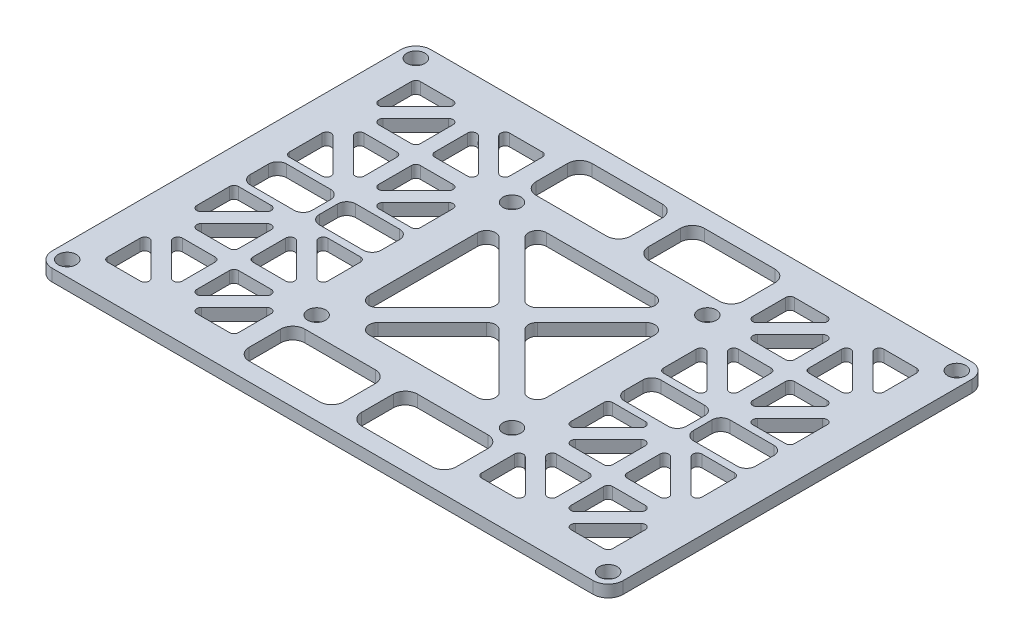
SolidWorks part; units mm, degrees
ref_plane "Front Plane" through (0, 0, 0) normal (0, 0, 1) x (1, 0, 0)
ref_plane "Top Plane" through (0, 0, 0) normal (0, 1, 0) x (1, 0, 0)
ref_plane "Right Plane" through (0, 0, 0) normal (1, 0, 0) x (0, 0, -1)
sketch "Sketch1" plane through (0, 0, 0) normal (0, 1, 0) x (1, 0, 0)
  line L1 (-45, -31.5) -> (45, -31.5)
  line L2 (-47.5, -29) -> (-47.5, 29)
  line L3 (-45, 31.5) -> (45, 31.5)
  line L4 (47.5, -29) -> (47.5, 29)
  line L5 (-47.5, -31.5) -> (47.5, 31.5) construction
  line L6 (-47.5, 31.5) -> (47.5, -31.5) construction
  circle A0 centre (45, 29) radius 1.5
  circle A1 centre (45, -29) radius 1.5
  circle A2 centre (-45, 29) radius 1.5
  circle A3 centre (-45, -29) radius 1.5
  arc A4 (-47.5, 29) -> (-45, 31.5) centre (-45, 29) cw
  arc A5 (-45, -31.5) -> (-47.5, -29) centre (-45, -29) cw
  arc A6 (45, -31.5) -> (47.5, -29) centre (45, -29) ccw
  arc A7 (45, 31.5) -> (47.5, 29) centre (45, 29) cw
  point P0 (0, 0)
  dimension "D3" = 3
  dimension "D5" = 2.5
  dimension "D1" = 95
  dimension "D2" = 63
extrude "Boss-Extrude1" add sketch "Sketch1" along normal blind 2
sketch "Sketch2" plane through (0, 2, 0) normal (0, 1, 0) x (1, 0, 0)
  line L0 (-12.1893, 10.068) -> (-3.182, 1.0607)
  line L1 (-16.25, -16.25) -> (16.25, -16.25) construction
  line L2 (-16.25, -16.25) -> (-16.25, 16.25) construction
  line L3 (-16.25, 16.25) -> (16.25, 16.25) construction
  line L4 (16.25, -16.25) -> (16.25, 16.25) construction
  line L5 (-16.25, -16.25) -> (16.25, 16.25) construction
  line L6 (-16.25, 16.25) -> (16.25, -16.25) construction
  line L7 (-3.182, -1.0607) -> (-12.1893, -10.068)
  line L8 (-14.75, -9.0074) -> (-14.75, 9.0074)
  line L9 (1.0607, 3.182) -> (10.068, 12.1893)
  line L10 (-10.068, 12.1893) -> (-1.0607, 3.182)
  line L11 (9.0074, 14.75) -> (-9.0074, 14.75)
  line L12 (3.182, 1.0607) -> (12.1893, 10.068)
  line L13 (14.75, 9.0074) -> (14.75, -9.0074)
  line L14 (12.1893, -10.068) -> (3.182, -1.0607)
  line L15 (-9.0074, -14.75) -> (9.0074, -14.75)
  line L16 (10.068, -12.1893) -> (1.0607, -3.182)
  line L17 (-1.0607, -3.182) -> (-10.068, -12.1893)
  line L18 (0, -31.5) -> (0, 31.5) construction
  line L19 (45, 31.5) -> (-45, 31.5) construction
  line L20 (35.8327, 26.0221) -> (41.2721, 26.0221)
  line L21 (42.0221, 25.2721) -> (42.0221, 19.8327)
  line L22 (40.7417, 19.3024) -> (35.3024, 24.7417)
  line L23 (33.6053, 23.0447) -> (39.0447, 17.6053)
  line L24 (38.5143, 16.325) -> (33.075, 16.325)
  line L25 (32.325, 17.075) -> (32.325, 22.5143)
  line L26 (31.125, 15.125) -> (14.75, 15.125) construction
  line L27 (40.325, 16.325) -> (42.0221, 18.0221) construction
  line L28 (33.075, 13.925) -> (38.5143, 13.925)
  line L29 (39.0447, 12.6447) -> (33.6053, 7.2053)
  line L30 (32.325, 7.7357) -> (32.325, 13.175)
  line L31 (35.3024, 5.5083) -> (40.7417, 10.9476)
  line L32 (42.0221, 10.4173) -> (42.0221, 4.9779)
  line L33 (41.2721, 4.2279) -> (35.8327, 4.2279)
  line L34 (29.925, 13.175) -> (29.925, 7.7357)
  line L35 (28.6447, 7.2053) -> (23.2053, 12.6447)
  line L36 (23.7357, 13.925) -> (29.175, 13.925)
  line L37 (21.5083, 10.9476) -> (26.9476, 5.5083)
  line L38 (26.4173, 4.2279) -> (20.9779, 4.2279)
  line L39 (20.2279, 4.9779) -> (20.2279, 10.4173)
  line L40 (29.175, 16.325) -> (23.7357, 16.325)
  line L41 (23.2053, 17.6053) -> (28.6447, 23.0447)
  line L42 (29.925, 22.5143) -> (29.925, 17.075)
  line L43 (26.9476, 24.7417) -> (21.5083, 19.3024)
  line L44 (20.2279, 19.8327) -> (20.2279, 25.2721)
  line L45 (20.9779, 26.0221) -> (26.4173, 26.0221)
  line L46 (31.125, 15.125) -> (47.5, 15.125) construction
  line L47 (-45, -31.5) -> (45, -31.5) construction
  line L48 (47.5, -29) -> (47.5, 29) construction
  line L49 (31.125, 15.125) -> (31.125, 31.5) construction
  line L50 (33.075, -16.325) -> (38.5143, -16.325)
  line L51 (39.0447, -17.6053) -> (33.6053, -23.0447)
  line L52 (32.325, -22.5143) -> (32.325, -17.075)
  line L53 (35.3024, -24.7417) -> (40.7417, -19.3024)
  line L54 (42.0221, -19.8327) -> (42.0221, -25.2721)
  line L55 (41.2721, -26.0221) -> (35.8327, -26.0221)
  line L56 (29.925, -17.075) -> (29.925, -22.5143)
  line L57 (28.6447, -23.0447) -> (23.2053, -17.6053)
  line L58 (23.7357, -16.325) -> (29.175, -16.325)
  line L59 (21.5083, -19.3024) -> (26.9476, -24.7417)
  line L60 (26.4173, -26.0221) -> (20.9779, -26.0221)
  line L61 (20.2279, -25.2721) -> (20.2279, -19.8327)
  line L62 (29.175, -13.925) -> (23.7357, -13.925)
  line L63 (23.2053, -12.6447) -> (28.6447, -7.2053)
  line L64 (29.925, -7.7357) -> (29.925, -13.175)
  line L65 (26.9476, -5.5083) -> (21.5083, -10.9476)
  line L66 (20.2279, -10.4173) -> (20.2279, -4.9779)
  line L67 (20.9779, -4.2279) -> (26.4173, -4.2279)
  line L68 (32.325, -13.175) -> (32.325, -7.7357)
  line L69 (33.6053, -7.2053) -> (39.0447, -12.6447)
  line L70 (38.5143, -13.925) -> (33.075, -13.925)
  line L71 (40.7417, -10.9476) -> (35.3024, -5.5083)
  line L72 (35.8327, -4.2279) -> (41.2721, -4.2279)
  line L73 (42.0221, -4.9779) -> (42.0221, -10.4173)
  line L74 (30.525, 0) -> (31.725, 0) construction
  line L81 (21.7279, -3.0279) -> (29.025, -3.0279)
  line L82 (20.2279, -1.5279) -> (20.2279, 1.5279)
  line L83 (21.7279, 3.0279) -> (29.025, 3.0279)
  line L84 (42.0221, -1.5279) -> (42.0221, 1.5279)
  line L85 (20.2279, -3.0279) -> (42.0221, 3.0279) construction
  line L86 (20.2279, 3.0279) -> (42.0221, -3.0279) construction
  line L87 (30.525, -1.5279) -> (30.525, 1.5279)
  line L88 (31.725, -1.5279) -> (31.725, 1.5279)
  line L89 (33.225, 3.0279) -> (40.5221, 3.0279)
  line L90 (33.225, -3.0279) -> (40.5221, -3.0279)
  line L91 (-20.2279, -25.2721) -> (-20.2279, -19.8327)
  line L92 (-26.4173, -26.0221) -> (-20.9779, -26.0221)
  line L93 (-21.5083, -19.3024) -> (-26.9476, -24.7417)
  line L94 (-41.2721, -26.0221) -> (-35.8327, -26.0221)
  line L95 (-42.0221, -19.8327) -> (-42.0221, -25.2721)
  line L96 (-35.3024, -24.7417) -> (-40.7417, -19.3024)
  line L97 (-32.325, -22.5143) -> (-32.325, -17.075)
  line L98 (-39.0447, -17.6053) -> (-33.6053, -23.0447)
  line L99 (-33.075, -16.325) -> (-38.5143, -16.325)
  line L100 (-23.7357, -16.325) -> (-29.175, -16.325)
  line L101 (-28.6447, -23.0447) -> (-23.2053, -17.6053)
  line L102 (-29.925, -17.075) -> (-29.925, -22.5143)
  line L103 (-20.9779, -4.2279) -> (-26.4173, -4.2279)
  line L104 (-20.2279, -10.4173) -> (-20.2279, -4.9779)
  line L105 (-26.9476, -5.5083) -> (-21.5083, -10.9476)
  line L106 (-29.925, -7.7357) -> (-29.925, -13.175)
  line L107 (-23.2053, -12.6447) -> (-28.6447, -7.2053)
  line L108 (-29.175, -13.925) -> (-23.7357, -13.925)
  line L109 (-38.5143, -13.925) -> (-33.075, -13.925)
  line L110 (-33.6053, -7.2053) -> (-39.0447, -12.6447)
  line L111 (-32.325, -13.175) -> (-32.325, -7.7357)
  line L112 (-42.0221, -4.9779) -> (-42.0221, -10.4173)
  line L113 (-35.8327, -4.2279) -> (-41.2721, -4.2279)
  line L114 (-40.7417, -10.9476) -> (-35.3024, -5.5083)
  line L115 (-33.225, -3.0279) -> (-40.5221, -3.0279)
  line L116 (-31.725, -1.5279) -> (-31.725, 1.5279)
  line L117 (-33.225, 3.0279) -> (-40.5221, 3.0279)
  line L118 (-42.0221, -1.5279) -> (-42.0221, 1.5279)
  line L119 (-20.2279, -1.5279) -> (-20.2279, 1.5279)
  line L120 (-21.7279, 3.0279) -> (-29.025, 3.0279)
  line L121 (-30.525, -1.5279) -> (-30.525, 1.5279)
  line L122 (-21.7279, -3.0279) -> (-29.025, -3.0279)
  line L123 (-20.2279, 4.9779) -> (-20.2279, 10.4173)
  line L124 (-26.4173, 4.2279) -> (-20.9779, 4.2279)
  line L125 (-21.5083, 10.9476) -> (-26.9476, 5.5083)
  line L126 (-41.2721, 4.2279) -> (-35.8327, 4.2279)
  line L127 (-42.0221, 10.4173) -> (-42.0221, 4.9779)
  line L128 (-35.3024, 5.5083) -> (-40.7417, 10.9476)
  line L129 (-23.7357, 13.925) -> (-29.175, 13.925)
  line L130 (-28.6447, 7.2053) -> (-23.2053, 12.6447)
  line L131 (-29.925, 13.175) -> (-29.925, 7.7357)
  line L132 (-32.325, 7.7357) -> (-32.325, 13.175)
  line L133 (-39.0447, 12.6447) -> (-33.6053, 7.2053)
  line L134 (-33.075, 13.925) -> (-38.5143, 13.925)
  line L135 (-42.0221, 25.2721) -> (-42.0221, 19.8327)
  line L136 (-35.8327, 26.0221) -> (-41.2721, 26.0221)
  line L137 (-40.7417, 19.3024) -> (-35.3024, 24.7417)
  line L138 (-38.5143, 16.325) -> (-33.075, 16.325)
  line L139 (-33.6053, 23.0447) -> (-39.0447, 17.6053)
  line L140 (-32.325, 17.075) -> (-32.325, 22.5143)
  line L141 (-29.925, 22.5143) -> (-29.925, 17.075)
  line L142 (-23.2053, 17.6053) -> (-28.6447, 23.0447)
  line L143 (-29.175, 16.325) -> (-23.7357, 16.325)
  line L144 (-20.9779, 26.0221) -> (-26.4173, 26.0221)
  line L145 (-20.2279, 19.8327) -> (-20.2279, 25.2721)
  line L146 (-26.9476, 24.7417) -> (-21.5083, 19.3024)
  line L147 (-17.2279, -19.25) -> (-17.2279, -16.25) construction
  line L148 (-15.2279, -28.5) -> (-3.5, -28.5)
  line L149 (-17.2279, -26.5) -> (-17.2279, -21.25)
  line L150 (-15.2279, -19.25) -> (-3.5, -19.25)
  line L151 (17.2279, -26.5) -> (17.2279, -21.25)
  line L152 (-17.2279, -28.5) -> (17.2279, -19.25) construction
  line L153 (-17.2279, -19.25) -> (17.2279, -28.5) construction
  line L154 (-17.2279, -28.5) -> (-17.2279, -31.5) construction
  line L155 (-1.5, -23.875) -> (1.5, -23.875) construction
  line L156 (-1.5, -26.5) -> (-1.5, -21.25)
  line L157 (1.5, -26.5) -> (1.5, -21.25)
  line L158 (3.5, -19.25) -> (15.2279, -19.25)
  line L159 (3.5, -28.5) -> (15.2279, -28.5)
  line L160 (3.5, 28.5) -> (15.2279, 28.5)
  line L161 (1.5, 26.5) -> (1.5, 21.25)
  line L162 (3.5, 19.25) -> (15.2279, 19.25)
  line L163 (17.2279, 26.5) -> (17.2279, 21.25)
  line L164 (-17.2279, 26.5) -> (-17.2279, 21.25)
  line L165 (-15.2279, 19.25) -> (-3.5, 19.25)
  line L166 (-1.5, 26.5) -> (-1.5, 21.25)
  line L167 (-15.2279, 28.5) -> (-3.5, 28.5)
  circle A0 centre (-16.25, 16.25) radius 1.5
  circle A1 centre (-16.25, -16.25) radius 1.5
  circle A2 centre (16.25, 16.25) radius 1.5
  circle A3 centre (16.25, -16.25) radius 1.5
  arc A4 (-14.75, -9.0074) -> (-12.1893, -10.068) centre (-13.25, -9.0074) ccw
  arc A5 (-3.182, -1.0607) -> (-3.182, 1.0607) centre (-4.2426, 0) ccw
  arc A6 (-12.1893, 10.068) -> (-14.75, 9.0074) centre (-13.25, 9.0074) ccw
  arc A7 (1.0607, 3.182) -> (-1.0607, 3.182) centre (0, 4.2426) cw
  arc A8 (9.0074, 14.75) -> (10.068, 12.1893) centre (9.0074, 13.25) cw
  arc A9 (-10.068, 12.1893) -> (-9.0074, 14.75) centre (-9.0074, 13.25) cw
  arc A10 (14.75, 9.0074) -> (12.1893, 10.068) centre (13.25, 9.0074) ccw
  arc A11 (12.1893, -10.068) -> (14.75, -9.0074) centre (13.25, -9.0074) ccw
  arc A12 (3.182, 1.0607) -> (3.182, -1.0607) centre (4.2426, 0) ccw
  arc A13 (10.068, -12.1893) -> (9.0074, -14.75) centre (9.0074, -13.25) cw
  arc A14 (-1.0607, -3.182) -> (1.0607, -3.182) centre (0, -4.2426) cw
  arc A15 (-9.0074, -14.75) -> (-10.068, -12.1893) centre (-9.0074, -13.25) cw
  arc A16 (33.075, 13.925) -> (32.325, 13.175) centre (33.075, 13.175) ccw
  circle A17 centre (45, 29) radius 1.5 construction
  circle A18 centre (45, 29) radius 1.5 construction
  arc A19 (40.7417, 19.3024) -> (42.0221, 19.8327) centre (41.2721, 19.8327) ccw
  arc A20 (42.0221, 25.2721) -> (41.2721, 26.0221) centre (41.2721, 25.2721) ccw
  arc A21 (35.8327, 26.0221) -> (35.3024, 24.7417) centre (35.8327, 25.2721) ccw
  arc A22 (32.325, 17.075) -> (33.075, 16.325) centre (33.075, 17.075) ccw
  arc A23 (38.5143, 16.325) -> (39.0447, 17.6053) centre (38.5143, 17.075) ccw
  arc A24 (33.6053, 23.0447) -> (32.325, 22.5143) centre (33.075, 22.5143) ccw
  arc A25 (20.9779, 26.0221) -> (20.2279, 25.2721) centre (20.9779, 25.2721) ccw
  arc A26 (20.2279, 19.8327) -> (21.5083, 19.3024) centre (20.9779, 19.8327) ccw
  arc A27 (26.9476, 24.7417) -> (26.4173, 26.0221) centre (26.4173, 25.2721) ccw
  arc A28 (28.6447, 23.0447) -> (29.925, 22.5143) centre (29.175, 22.5143) cw
  arc A29 (29.925, 17.075) -> (29.175, 16.325) centre (29.175, 17.075) cw
  arc A30 (23.7357, 16.325) -> (23.2053, 17.6053) centre (23.7357, 17.075) cw
  arc A31 (20.2279, 4.9779) -> (20.9779, 4.2279) centre (20.9779, 4.9779) ccw
  arc A32 (26.4173, 4.2279) -> (26.9476, 5.5083) centre (26.4173, 4.9779) ccw
  arc A33 (21.5083, 10.9476) -> (20.2279, 10.4173) centre (20.9779, 10.4173) ccw
  arc A34 (23.7357, 13.925) -> (23.2053, 12.6447) centre (23.7357, 13.175) ccw
  arc A35 (28.6447, 7.2053) -> (29.925, 7.7357) centre (29.175, 7.7357) ccw
  arc A36 (29.925, 13.175) -> (29.175, 13.925) centre (29.175, 13.175) ccw
  arc A37 (40.7417, 10.9476) -> (42.0221, 10.4173) centre (41.2721, 10.4173) cw
  arc A38 (42.0221, 4.9779) -> (41.2721, 4.2279) centre (41.2721, 4.9779) cw
  arc A39 (35.8327, 4.2279) -> (35.3024, 5.5083) centre (35.8327, 4.9779) cw
  arc A40 (32.325, 7.7357) -> (33.6053, 7.2053) centre (33.075, 7.7357) ccw
  arc A41 (39.0447, 12.6447) -> (38.5143, 13.925) centre (38.5143, 13.175) ccw
  arc A42 (39.0447, -17.6053) -> (38.5143, -16.325) centre (38.5143, -17.075) ccw
  arc A43 (33.075, -16.325) -> (32.325, -17.075) centre (33.075, -17.075) ccw
  arc A44 (32.325, -22.5143) -> (33.6053, -23.0447) centre (33.075, -22.5143) ccw
  arc A45 (35.8327, -26.0221) -> (35.3024, -24.7417) centre (35.8327, -25.2721) cw
  arc A46 (40.7417, -19.3024) -> (42.0221, -19.8327) centre (41.2721, -19.8327) cw
  arc A47 (42.0221, -25.2721) -> (41.2721, -26.0221) centre (41.2721, -25.2721) cw
  arc A48 (29.925, -17.075) -> (29.175, -16.325) centre (29.175, -17.075) ccw
  arc A49 (28.6447, -23.0447) -> (29.925, -22.5143) centre (29.175, -22.5143) ccw
  arc A50 (23.7357, -16.325) -> (23.2053, -17.6053) centre (23.7357, -17.075) ccw
  arc A51 (21.5083, -19.3024) -> (20.2279, -19.8327) centre (20.9779, -19.8327) ccw
  arc A52 (26.4173, -26.0221) -> (26.9476, -24.7417) centre (26.4173, -25.2721) ccw
  arc A53 (20.2279, -25.2721) -> (20.9779, -26.0221) centre (20.9779, -25.2721) ccw
  arc A54 (23.7357, -13.925) -> (23.2053, -12.6447) centre (23.7357, -13.175) cw
  arc A55 (29.925, -13.175) -> (29.175, -13.925) centre (29.175, -13.175) cw
  arc A56 (28.6447, -7.2053) -> (29.925, -7.7357) centre (29.175, -7.7357) cw
  arc A57 (26.9476, -5.5083) -> (26.4173, -4.2279) centre (26.4173, -4.9779) ccw
  arc A58 (20.2279, -10.4173) -> (21.5083, -10.9476) centre (20.9779, -10.4173) ccw
  arc A59 (20.9779, -4.2279) -> (20.2279, -4.9779) centre (20.9779, -4.9779) ccw
  arc A60 (33.6053, -7.2053) -> (32.325, -7.7357) centre (33.075, -7.7357) ccw
  arc A61 (32.325, -13.175) -> (33.075, -13.925) centre (33.075, -13.175) ccw
  arc A62 (38.5143, -13.925) -> (39.0447, -12.6447) centre (38.5143, -13.175) ccw
  arc A63 (35.8327, -4.2279) -> (35.3024, -5.5083) centre (35.8327, -4.9779) ccw
  arc A64 (40.7417, -10.9476) -> (42.0221, -10.4173) centre (41.2721, -10.4173) ccw
  arc A65 (42.0221, -4.9779) -> (41.2721, -4.2279) centre (41.2721, -4.9779) ccw
  arc A66 (31.725, -1.5279) -> (33.225, -3.0279) centre (33.225, -1.5279) ccw
  arc A67 (40.5221, -3.0279) -> (42.0221, -1.5279) centre (40.5221, -1.5279) ccw
  arc A68 (42.0221, 1.5279) -> (40.5221, 3.0279) centre (40.5221, 1.5279) ccw
  arc A69 (33.225, 3.0279) -> (31.725, 1.5279) centre (33.225, 1.5279) ccw
  arc A70 (20.2279, -1.5279) -> (21.7279, -3.0279) centre (21.7279, -1.5279) ccw
  arc A71 (29.025, -3.0279) -> (30.525, -1.5279) centre (29.025, -1.5279) ccw
  arc A72 (30.525, 1.5279) -> (29.025, 3.0279) centre (29.025, 1.5279) ccw
  arc A73 (21.7279, 3.0279) -> (20.2279, 1.5279) centre (21.7279, 1.5279) ccw
  arc A74 (-21.5083, -19.3024) -> (-20.2279, -19.8327) centre (-20.9779, -19.8327) cw
  arc A75 (-20.2279, -25.2721) -> (-20.9779, -26.0221) centre (-20.9779, -25.2721) cw
  arc A76 (-26.4173, -26.0221) -> (-26.9476, -24.7417) centre (-26.4173, -25.2721) cw
  arc A77 (-35.8327, -26.0221) -> (-35.3024, -24.7417) centre (-35.8327, -25.2721) ccw
  arc A78 (-42.0221, -25.2721) -> (-41.2721, -26.0221) centre (-41.2721, -25.2721) ccw
  arc A79 (-40.7417, -19.3024) -> (-42.0221, -19.8327) centre (-41.2721, -19.8327) ccw
  arc A80 (-33.075, -16.325) -> (-32.325, -17.075) centre (-33.075, -17.075) cw
  arc A81 (-32.325, -22.5143) -> (-33.6053, -23.0447) centre (-33.075, -22.5143) cw
  arc A82 (-39.0447, -17.6053) -> (-38.5143, -16.325) centre (-38.5143, -17.075) cw
  arc A83 (-29.925, -17.075) -> (-29.175, -16.325) centre (-29.175, -17.075) cw
  arc A84 (-23.7357, -16.325) -> (-23.2053, -17.6053) centre (-23.7357, -17.075) cw
  arc A85 (-28.6447, -23.0447) -> (-29.925, -22.5143) centre (-29.175, -22.5143) cw
  arc A86 (-26.9476, -5.5083) -> (-26.4173, -4.2279) centre (-26.4173, -4.9779) cw
  arc A87 (-20.9779, -4.2279) -> (-20.2279, -4.9779) centre (-20.9779, -4.9779) cw
  arc A88 (-20.2279, -10.4173) -> (-21.5083, -10.9476) centre (-20.9779, -10.4173) cw
  arc A89 (-29.925, -13.175) -> (-29.175, -13.925) centre (-29.175, -13.175) ccw
  arc A90 (-28.6447, -7.2053) -> (-29.925, -7.7357) centre (-29.175, -7.7357) ccw
  arc A91 (-23.7357, -13.925) -> (-23.2053, -12.6447) centre (-23.7357, -13.175) ccw
  arc A92 (-32.325, -13.175) -> (-33.075, -13.925) centre (-33.075, -13.175) cw
  arc A93 (-38.5143, -13.925) -> (-39.0447, -12.6447) centre (-38.5143, -13.175) cw
  arc A94 (-33.6053, -7.2053) -> (-32.325, -7.7357) centre (-33.075, -7.7357) cw
  arc A95 (-40.7417, -10.9476) -> (-42.0221, -10.4173) centre (-41.2721, -10.4173) cw
  arc A96 (-42.0221, -4.9779) -> (-41.2721, -4.2279) centre (-41.2721, -4.9779) cw
  arc A97 (-35.8327, -4.2279) -> (-35.3024, -5.5083) centre (-35.8327, -4.9779) cw
  arc A98 (-31.725, -1.5279) -> (-33.225, -3.0279) centre (-33.225, -1.5279) cw
  arc A99 (-33.225, 3.0279) -> (-31.725, 1.5279) centre (-33.225, 1.5279) cw
  arc A100 (-40.5221, -3.0279) -> (-42.0221, -1.5279) centre (-40.5221, -1.5279) cw
  arc A101 (-42.0221, 1.5279) -> (-40.5221, 3.0279) centre (-40.5221, 1.5279) cw
  arc A102 (-21.7279, 3.0279) -> (-20.2279, 1.5279) centre (-21.7279, 1.5279) cw
  arc A103 (-30.525, 1.5279) -> (-29.025, 3.0279) centre (-29.025, 1.5279) cw
  arc A104 (-20.2279, -1.5279) -> (-21.7279, -3.0279) centre (-21.7279, -1.5279) cw
  arc A105 (-29.025, -3.0279) -> (-30.525, -1.5279) centre (-29.025, -1.5279) cw
  arc A106 (-20.2279, 4.9779) -> (-20.9779, 4.2279) centre (-20.9779, 4.9779) cw
  arc A107 (-26.4173, 4.2279) -> (-26.9476, 5.5083) centre (-26.4173, 4.9779) cw
  arc A108 (-21.5083, 10.9476) -> (-20.2279, 10.4173) centre (-20.9779, 10.4173) cw
  arc A109 (-42.0221, 4.9779) -> (-41.2721, 4.2279) centre (-41.2721, 4.9779) ccw
  arc A110 (-40.7417, 10.9476) -> (-42.0221, 10.4173) centre (-41.2721, 10.4173) ccw
  arc A111 (-35.8327, 4.2279) -> (-35.3024, 5.5083) centre (-35.8327, 4.9779) ccw
  arc A112 (-23.7357, 13.925) -> (-23.2053, 12.6447) centre (-23.7357, 13.175) cw
  arc A113 (-28.6447, 7.2053) -> (-29.925, 7.7357) centre (-29.175, 7.7357) cw
  arc A114 (-29.925, 13.175) -> (-29.175, 13.925) centre (-29.175, 13.175) cw
  arc A115 (-32.325, 7.7357) -> (-33.6053, 7.2053) centre (-33.075, 7.7357) cw
  arc A116 (-33.075, 13.925) -> (-32.325, 13.175) centre (-33.075, 13.175) cw
  arc A117 (-39.0447, 12.6447) -> (-38.5143, 13.925) centre (-38.5143, 13.175) cw
  arc A118 (-42.0221, 25.2721) -> (-41.2721, 26.0221) centre (-41.2721, 25.2721) cw
  arc A119 (-40.7417, 19.3024) -> (-42.0221, 19.8327) centre (-41.2721, 19.8327) cw
  arc A120 (-35.8327, 26.0221) -> (-35.3024, 24.7417) centre (-35.8327, 25.2721) cw
  arc A121 (-38.5143, 16.325) -> (-39.0447, 17.6053) centre (-38.5143, 17.075) cw
  arc A122 (-32.325, 17.075) -> (-33.075, 16.325) centre (-33.075, 17.075) cw
  arc A123 (-33.6053, 23.0447) -> (-32.325, 22.5143) centre (-33.075, 22.5143) cw
  arc A124 (-28.6447, 23.0447) -> (-29.925, 22.5143) centre (-29.175, 22.5143) ccw
  arc A125 (-29.925, 17.075) -> (-29.175, 16.325) centre (-29.175, 17.075) ccw
  arc A126 (-23.7357, 16.325) -> (-23.2053, 17.6053) centre (-23.7357, 17.075) ccw
  arc A127 (-20.9779, 26.0221) -> (-20.2279, 25.2721) centre (-20.9779, 25.2721) cw
  arc A128 (-20.2279, 19.8327) -> (-21.5083, 19.3024) centre (-20.9779, 19.8327) cw
  arc A129 (-26.9476, 24.7417) -> (-26.4173, 26.0221) centre (-26.4173, 25.2721) cw
  arc A130 (-17.2279, -26.5) -> (-15.2279, -28.5) centre (-15.2279, -26.5) ccw
  arc A131 (-3.5, -28.5) -> (-1.5, -26.5) centre (-3.5, -26.5) ccw
  arc A132 (-1.5, -21.25) -> (-3.5, -19.25) centre (-3.5, -21.25) ccw
  arc A133 (-15.2279, -19.25) -> (-17.2279, -21.25) centre (-15.2279, -21.25) ccw
  arc A134 (15.2279, -19.25) -> (17.2279, -21.25) centre (15.2279, -21.25) cw
  arc A135 (17.2279, -26.5) -> (15.2279, -28.5) centre (15.2279, -26.5) cw
  arc A136 (3.5, -28.5) -> (1.5, -26.5) centre (3.5, -26.5) cw
  arc A137 (3.5, -19.25) -> (1.5, -21.25) centre (3.5, -21.25) ccw
  arc A138 (3.5, 28.5) -> (1.5, 26.5) centre (3.5, 26.5) ccw
  arc A139 (3.5, 19.25) -> (1.5, 21.25) centre (3.5, 21.25) cw
  arc A140 (15.2279, 19.25) -> (17.2279, 21.25) centre (15.2279, 21.25) ccw
  arc A141 (17.2279, 26.5) -> (15.2279, 28.5) centre (15.2279, 26.5) ccw
  arc A142 (-15.2279, 19.25) -> (-17.2279, 21.25) centre (-15.2279, 21.25) cw
  arc A143 (-1.5, 21.25) -> (-3.5, 19.25) centre (-3.5, 21.25) cw
  arc A144 (-17.2279, 26.5) -> (-15.2279, 28.5) centre (-15.2279, 26.5) cw
  arc A145 (-3.5, 28.5) -> (-1.5, 26.5) centre (-3.5, 26.5) cw
  point P0 (0, 0)
  point P51 (0, 0)
  point P59 (31.125, 15.125)
  point P81 (31.125, 15.125)
  point P93 (42.0221, 26.0221)
  point P96 (34.0221, 26.0221)
  point P212 (31.125, 0)
  point P220 (31.125, 0)
  point P223 (30.525, 0)
  point P226 (31.725, 0)
  point P236 (31.725, 3.0279)
  point P415 (0, -23.875)
  point P424 (0, -23.875)
  point P428 (-1.5, -23.875)
  point P431 (1.5, -23.875)
  point P451 (1.5, -19.25)
  dimension "D2" = 3
  dimension "D6" = 1.5
  dimension "D9" = 0.75
  dimension "D13" = 0.75
  dimension "D19" = 1.5
  dimension "D23" = 2
  dimension "D24" = 2
  dimension "D1" = 32.5
  dimension "D3" = 3
  dimension "D4" = 3
  dimension "D5" = 3
  dimension "D7" = 2.4
  dimension "D8" = 8
  dimension "D10" = 1.2
  dimension "D11" = 1.2
  dimension "D15" = 5.4779
  dimension "D16" = 5.4779
  dimension "D17" = 1.2
  dimension "D18" = 1.2
  dimension "D20" = 3
  dimension "D21" = 3
  dimension "D22" = 3
  dimension "D14" = 2
  dimension "D12" = 4
extrude "Cut-Extrude1" cut sketch "Sketch2" against normal through all
equation "\"D4@Sketch2\"=\"D3@Sketch2\""
equation "\"D5@Sketch2\"=\"D3@Sketch2\""
equation "\"D11@Sketch2\"=\"D7@Sketch2\"/2"
equation "\"D10@Sketch2\"=\"D11@Sketch2\""
equation "\"D7@Sketch2\"=\"D8@Sketch2\"/5*1.5"
equation "\"D16@Sketch2\"=\"D15@Sketch2\""
equation "\"D17@Sketch2\"=\"D10@Sketch2\""
equation "\"D18@Sketch2\"=\"D17@Sketch2\""
